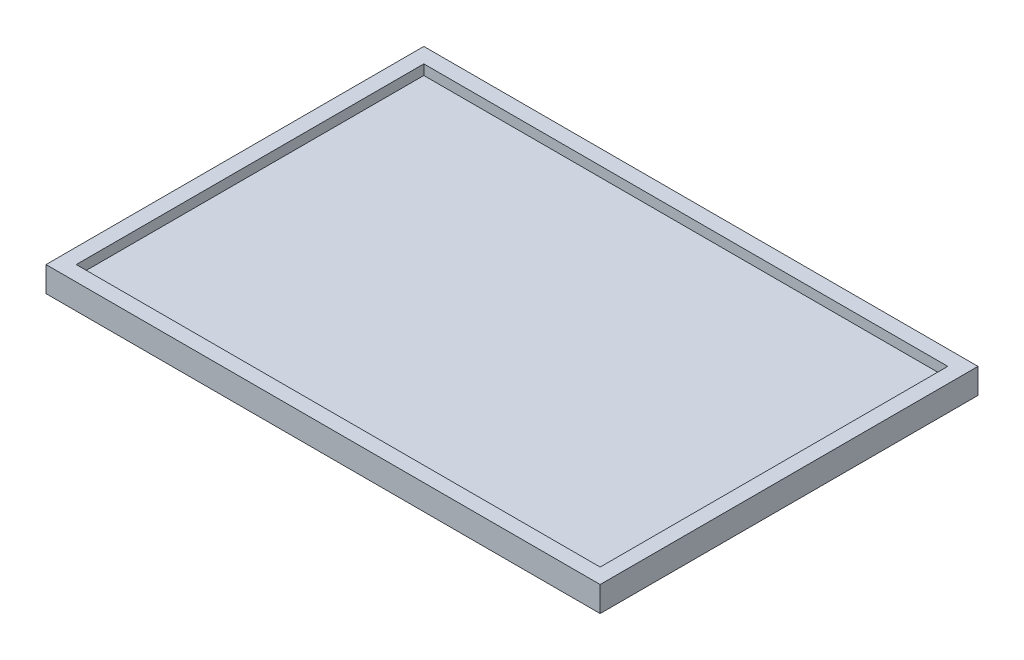
SolidWorks part; units mm, degrees
ref_plane "Front Plane" through (0, 0, 0) normal (0, 0, 1) x (1, 0, 0)
ref_plane "Top Plane" through (0, 0, 0) normal (0, 1, 0) x (1, 0, 0)
ref_plane "Right Plane" through (0, 0, 0) normal (1, 0, 0) x (0, 0, -1)
sketch "Sketch1" plane through (0, 0, 0) normal (0, 1, 0) x (1, 0, 0)
  line L1 (-49.8344, 19.8116) -> (60.1656, 19.8116)
  line L2 (-49.8344, 19.8116) -> (-49.8344, -55.1884)
  line L3 (-49.8344, -55.1884) -> (60.1656, -55.1884)
  line L4 (60.1656, 19.8116) -> (60.1656, -55.1884)
  dimension "D1" = 110
  dimension "D2" = 75
extrude "Boss-Extrude1" add sketch "Sketch1" along normal blind 5
sketch "Sketch2" plane through (0, 5, 0) normal (0, 1, 0) x (1, 0, 0)
  line L12 (-46.8344, 16.8116) -> (-46.8344, -52.1884)
  line L13 (-46.8344, -52.1884) -> (57.1656, -52.1884)
  line L14 (57.1656, -52.1884) -> (57.1656, 16.8116)
  line L15 (57.1656, 16.8116) -> (-46.8344, 16.8116)
  line L16 (-46.8344, 16.8116) -> (-46.8344, -52.1884)
  line L17 (-46.8344, -52.1884) -> (57.1656, -52.1884)
  line L18 (57.1656, -52.1884) -> (57.1656, 16.8116)
  line L19 (57.1656, 16.8116) -> (-46.8344, 16.8116)
  dimension "D1" = 3
extrude "Cut-Extrude1" cut sketch "Sketch2" against normal blind 2
